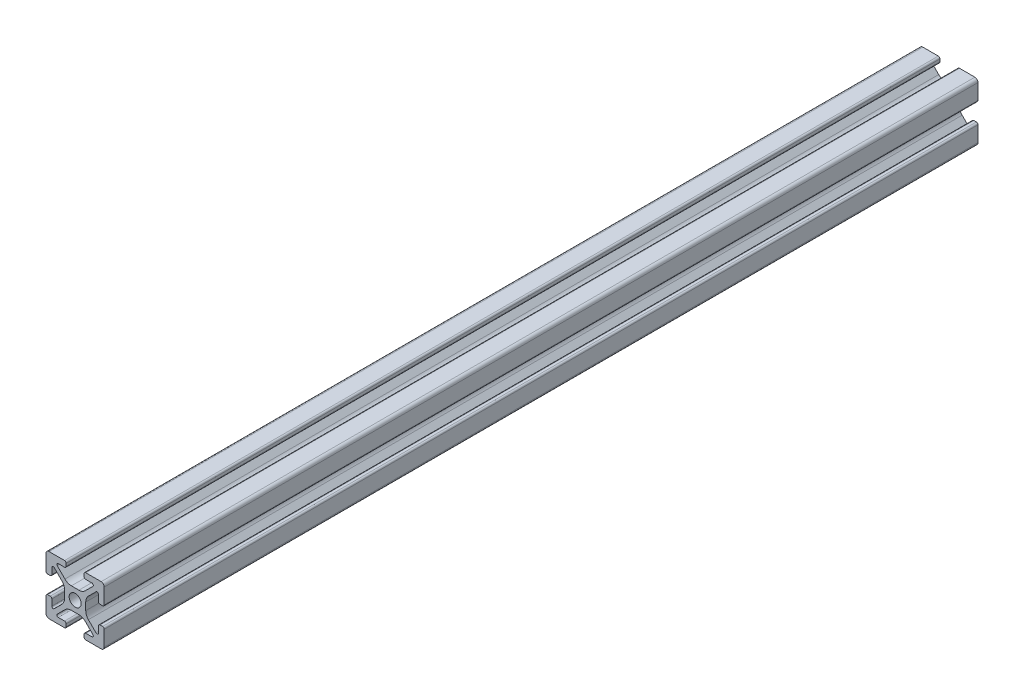
SolidWorks part; units mm, degrees
ref_plane "Front Plane" through (0, 0, 0) normal (0, 0, 1) x (1, 0, 0)
ref_plane "Top Plane" through (0, 0, 0) normal (0, 1, 0) x (1, 0, 0)
ref_plane "Right Plane" through (0, 0, 0) normal (1, 0, 0) x (0, 0, -1)
sketch "Sketch2" plane through (0, 0, 0) normal (0, 0, 1) x (1, 0, 0)
  line L0 (-3.6422, 1.2878) -> (-3.6422, -1.2878)
  line L1 (-1.2878, 3.6422) -> (1.2878, 3.6422)
  line L2 (-9.4433, 3.069) -> (-8.553, 3.069)
  line L3 (0, 0) -> (-15.7854, 0) construction
  line L4 (-3.4964, 4.5571) -> (-6.1213, 7.182)
  line L5 (-3.622, 8) -> (-5.7825, 8)
  line L6 (-3.069, 9.4433) -> (-3.069, 8.553)
  line L7 (-3.622, 10) -> (-8.939, 10)
  line L8 (0, 0) -> (0, 15.0393) construction
  line L9 (10, 3.622) -> (10, 8.939)
  line L10 (8, 3.622) -> (8, 5.7825)
  line L11 (4.5571, 3.4964) -> (7.182, 6.1213)
  line L12 (3.622, 10) -> (8.939, 10)
  line L13 (3.069, 9.4433) -> (3.069, 8.553)
  line L14 (3.622, 8) -> (5.7825, 8)
  line L15 (3.4964, 4.5571) -> (6.1213, 7.182)
  line L16 (9.4433, 3.069) -> (8.553, 3.069)
  line L17 (3.6422, 1.2878) -> (3.6422, -1.2878)
  line L18 (-10, -3.622) -> (-10, -8.939)
  line L19 (-8, -3.622) -> (-8, -5.7825)
  line L20 (-4.5571, -3.4964) -> (-7.182, -6.1213)
  line L21 (9.4433, -3.069) -> (8.553, -3.069)
  line L22 (3.4964, -4.5571) -> (6.1213, -7.182)
  line L23 (3.622, -8) -> (5.7825, -8)
  line L24 (3.069, -9.4433) -> (3.069, -8.553)
  line L25 (3.622, -10) -> (8.939, -10)
  line L26 (4.5571, -3.4964) -> (7.182, -6.1213)
  line L27 (8, -3.622) -> (8, -5.7825)
  line L28 (10, -3.622) -> (10, -8.939)
  line L29 (-3.622, -10) -> (-8.939, -10)
  line L30 (-3.069, -9.4433) -> (-3.069, -8.553)
  line L31 (-3.622, -8) -> (-5.7825, -8)
  line L32 (-3.4964, -4.5571) -> (-6.1213, -7.182)
  line L33 (-9.4433, -3.069) -> (-8.553, -3.069)
  line L34 (-1.2878, -3.6422) -> (1.2878, -3.6422)
  line L48 (-4.5571, 3.4964) -> (-7.182, 6.1213)
  line L49 (-8, 3.622) -> (-8, 5.7825)
  line L52 (-10, 3.622) -> (-10, 8.939)
  arc A0 (-8.553, 3.069) -> (-8, 3.622) centre (-8.553, 3.622) ccw
  arc A1 (-8, 5.7825) -> (-7.182, 6.1213) centre (-7.5208, 5.7825) cw
  arc A2 (-4.5571, 3.4964) -> (-3.6422, 1.2878) centre (-6.7657, 1.2878) cw
  arc A3 (-3.4964, 4.5571) -> (-1.2878, 3.6422) centre (-1.2878, 6.7657) ccw
  arc A4 (-5.7825, 8) -> (-6.1213, 7.182) centre (-5.7825, 7.5208) ccw
  arc A5 (-3.622, 10) -> (-3.069, 9.4433) centre (-3.622, 9.447) cw
  arc A6 (-3.069, 8.553) -> (-3.622, 8) centre (-3.622, 8.553) cw
  arc A7 (8.939, 10) -> (10, 8.939) centre (8.939, 8.939) cw
  arc A8 (10, 3.622) -> (9.4433, 3.069) centre (9.447, 3.622) cw
  arc A9 (3.069, 8.553) -> (3.622, 8) centre (3.622, 8.553) ccw
  arc A10 (3.622, 10) -> (3.069, 9.4433) centre (3.622, 9.447) ccw
  arc A11 (5.7825, 8) -> (6.1213, 7.182) centre (5.7825, 7.5208) cw
  arc A12 (3.4964, 4.5571) -> (1.2878, 3.6422) centre (1.2878, 6.7657) cw
  arc A13 (4.5571, 3.4964) -> (3.6422, 1.2878) centre (6.7657, 1.2878) ccw
  arc A14 (8, 5.7825) -> (7.182, 6.1213) centre (7.5208, 5.7825) ccw
  arc A15 (8.553, 3.069) -> (8, 3.622) centre (8.553, 3.622) cw
  arc A16 (-8.939, -10) -> (-10, -8.939) centre (-8.939, -8.939) cw
  arc A17 (-10, -3.622) -> (-9.4433, -3.069) centre (-9.447, -3.622) cw
  arc A18 (8.553, -3.069) -> (8, -3.622) centre (8.553, -3.622) ccw
  arc A19 (8, -5.7825) -> (7.182, -6.1213) centre (7.5208, -5.7825) cw
  arc A20 (4.5571, -3.4964) -> (3.6422, -1.2878) centre (6.7657, -1.2878) cw
  arc A21 (3.4964, -4.5571) -> (1.2878, -3.6422) centre (1.2878, -6.7657) ccw
  arc A22 (5.7825, -8) -> (6.1213, -7.182) centre (5.7825, -7.5208) ccw
  arc A23 (3.622, -10) -> (3.069, -9.4433) centre (3.622, -9.447) cw
  arc A24 (3.069, -8.553) -> (3.622, -8) centre (3.622, -8.553) cw
  arc A25 (10, -3.622) -> (9.4433, -3.069) centre (9.447, -3.622) ccw
  arc A26 (8.939, -10) -> (10, -8.939) centre (8.939, -8.939) ccw
  arc A27 (-3.069, -8.553) -> (-3.622, -8) centre (-3.622, -8.553) ccw
  arc A28 (-3.622, -10) -> (-3.069, -9.4433) centre (-3.622, -9.447) ccw
  arc A29 (-5.7825, -8) -> (-6.1213, -7.182) centre (-5.7825, -7.5208) cw
  arc A30 (-3.4964, -4.5571) -> (-1.2878, -3.6422) centre (-1.2878, -6.7657) cw
  arc A31 (-4.5571, -3.4964) -> (-3.6422, -1.2878) centre (-6.7657, -1.2878) ccw
  arc A32 (-8, -5.7825) -> (-7.182, -6.1213) centre (-7.5208, -5.7825) ccw
  arc A33 (-8.553, -3.069) -> (-8, -3.622) centre (-8.553, -3.622) cw
  arc A51 (-10, 3.622) -> (-9.4433, 3.069) centre (-9.447, 3.622) ccw
  arc A56 (-8.939, 10) -> (-10, 8.939) centre (-8.939, 8.939) ccw
  circle A57 centre (0, 0) radius 2.05
  point P1 (-3.6422, 0)
  point P46 (0, 0)
  point P48 (0, 0)
  point P53 (0, 3.6422)
  point P60 (0, 0)
  point P61 (0, 0)
  point P62 (0, 0)
  point P74 (0, 0)
  point P85 (0, 0)
  point P87 (0, 0)
  point P99 (0, 0)
  point P101 (0, 0)
  point P102 (0, 0)
  point P116 (0, -3.6422)
  point P117 (3.6422, 0)
  point P123 (0, 0)
  point P125 (0, 0)
  point P127 (0, 0)
  point P139 (0, 0)
  point P140 (0, 0)
  point P141 (0, 0)
  point P142 (0, 0)
  point P179 (0, 0)
  point P192 (0, 0)
  point P193 (0, 0)
  dimension "D1" = 0.553
  dimension "D3" = 3.1235
  dimension "D4" = 0.553
  dimension "D2" = 0.4792
  dimension "D5" = 1.061
  dimension "D6" = 2.05
extrude "Boss-Extrude1" add sketch "Sketch2" against normal blind 300
